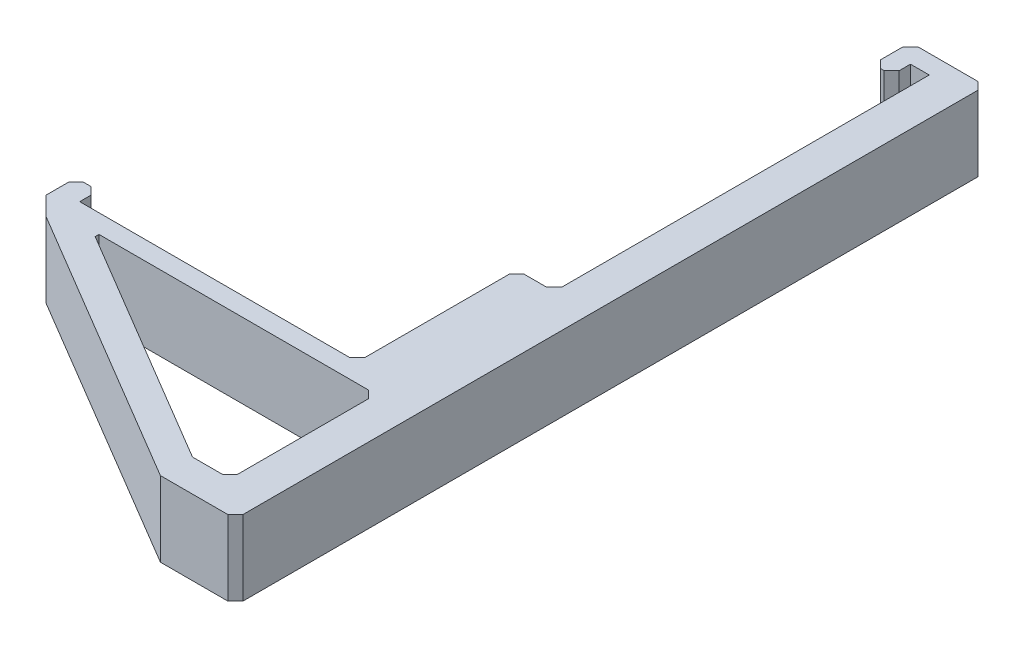
SolidWorks part; units mm, degrees
ref_plane "Front Plane" through (0, 0, 0) normal (0, 0, 1) x (1, 0, 0)
ref_plane "Top Plane" through (0, 0, 0) normal (0, 1, 0) x (1, 0, 0)
ref_plane "Right Plane" through (0, 0, 0) normal (1, 0, 0) x (0, 0, -1)
sketch "Sketch1" plane through (0, 0, 0) normal (0, 1, 0) x (1, 0, 0)
  line L0 (0, 0) -> (0, 45)
  line L1 (-5, -50) -> (5, -50)
  line L3 (-5, 50) -> (5, 50)
  line L4 (5, -50) -> (5, 50)
  line L5 (0, 0) -> (0, -2.5)
  line L6 (-5, 45) -> (-5, 50)
  line L7 (-2.5, 45) -> (-5, 45)
  line L10 (0, 45) -> (0, 47.5)
  line L11 (0, 47.5) -> (-2.5, 47.5)
  line L12 (-2.5, 45) -> (-2.5, 47.5)
  line L15 (0, -2.5) -> (-5, -2.5)
  line L17 (-5, -2.5) -> (-5, -21.25)
  line L19 (-45, -26.25) -> (-5, -50)
  line L20 (-37.7936, -26.25) -> (-5, -45.7212)
  line L22 (-45, -26.25) -> (-45, -21.25)
  line L23 (-45, -21.25) -> (-42.0041, -21.25)
  line L26 (-5, -21.25) -> (-5, -23.75)
  line L27 (-5, -23.75) -> (-42.0041, -23.75)
  line L28 (-42.0041, -21.25) -> (-42.0041, -23.75)
  line L29 (-37.7936, -26.25) -> (0, -26.25)
  line L30 (0, -26.25) -> (0, -45.7212)
  line L31 (-5, -45.7212) -> (0, -45.7212)
  point P0 (0, 0)
  dimension "D1" = 100
  dimension "D2" = 10
extrude "Boss-Extrude1" add sketch "Sketch1" along normal blind 10
chamfer "Chamfer1" distance 1 angle 60 1 edges at (-37.7936, 5, 26.25)
chamfer "Chamfer2" distance 1 angle 45 13 edges at (-42.0041, 5, 21.25) (5, 5, 50) (5, 5, -50) (-5, 5, -50) (-2.5, 5, -45) (-5, 5, -45) (0, 5, 2.5) (-5, 5, 2.5) (0, 5, 45.7212) (0, 5, 26.25) (-5, 5, 23.75) (-45, 5, 26.25) (-45, 5, 21.25)
